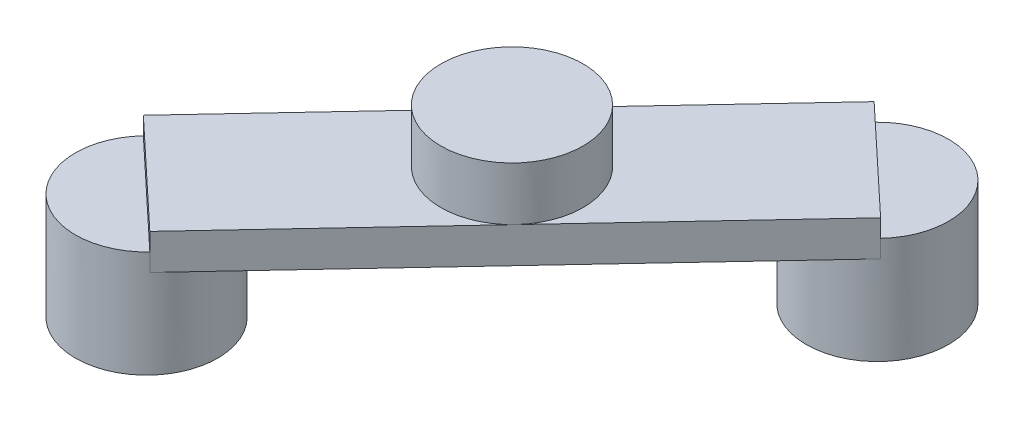
SolidWorks part; units mm, degrees
ref_plane "Front Plane" through (0, 0, 0) normal (0, 0, 1) x (1, 0, 0)
ref_plane "Top Plane" through (0, 0, 0) normal (0, 1, 0) x (1, 0, 0)
ref_plane "Right Plane" through (0, 0, 0) normal (1, 0, 0) x (0, 0, -1)
sketch "Sketch1" plane through (0, 0, 0) normal (0, 1, 0) x (1, 0, 0)
  line L0 (0, 0) -> (14.8833, -1.8676) construction
  line L1 (-14.2765, 6.7034) -> (-15.4901, -2.9683)
  line L2 (-15.4901, -2.9683) -> (-10.787, -11.5063)
  line L3 (-10.787, -11.5063) -> (-1.9637, -15.6492)
  line L4 (-1.9637, -15.6492) -> (7.6097, -13.8147)
  line L5 (7.6097, -13.8147) -> (14.2765, -6.7034)
  line L6 (14.2765, -6.7034) -> (15.4901, 2.9683)
  line L7 (15.4901, 2.9683) -> (10.787, 11.5063)
  line L8 (10.787, 11.5063) -> (1.9637, 15.6492)
  line L9 (1.9637, 15.6492) -> (-7.6097, 13.8147)
  line L10 (-7.6097, 13.8147) -> (-14.2765, 6.7034)
  line L11 (14.8833, -1.8676) -> (21.4363, -2.6898) construction
  line L12 (0, 0) -> (2.823, -14.732) construction
  line L13 (2.823, -14.732) -> (3.8609, -20.1481) construction
  line L14 (2.3263, -12.1398) -> (12.2645, -1.5389) construction
  circle A0 centre (0, 0) radius 15 construction
  circle A1 centre (2.3263, -12.1398) radius 2
  circle A2 centre (12.2645, -1.5389) radius 2
  dimension "D2" = 4
  dimension "D3" = 4
  dimension "D1" = 30
  dimension "D4" = 5
extrude "Boss-Extrude1" add sketch "Sketch1" along normal blind 3 contours A1 | A2
ref_plane "Plane1" through (8.7545, 0, 8.2072) normal (0.7295, 0, 0.6839) x (0.6839, 0, -0.7295)
sketch "Sketch2" plane through (8.7545, 0, 8.2072) normal (0.7295, 0, 0.6839) x (0.6839, 0, -0.7295)
  line L0 (9.2654, 3) -> (5.2654, 3) construction
  line L5 (9.2654, 3) -> (5.2654, 3)
  line L6 (-7.2654, 3) -> (7.2654, 3)
  line L7 (-5.2654, 3) -> (-9.2654, 3) construction
  line L9 (-7.2654, 2.5) -> (7.2654, 2.5)
  line L10 (-7.2654, 2.5) -> (-7.2654, 3.5)
  line L11 (-7.2654, 3.5) -> (7.2654, 3.5)
  line L12 (7.2654, 2.5) -> (7.2654, 3.5)
  line L13 (-7.2654, 2.5) -> (7.2654, 3.5) construction
  line L14 (-7.2654, 3.5) -> (7.2654, 2.5) construction
  point P0 (0, 3.0774)
  point P7 (0, 3)
  dimension "D1" = 1
extrude "Boss-Extrude2" add sketch "Sketch2" against normal blind 4 contours L5 L12 L11 L10 L6 | L9 L12 L5 L6 L10
sketch "Sketch4" plane through (0, 3.5, 0) normal (0, 1, 0) x (1, 0, 0)
  line L0 (0.8672, -10.7719) -> (3.7854, -13.5077) construction
  line L1 (0.8672, -10.7719) -> (10.8054, -0.1711) construction
  line L2 (0.8672, -10.7719) -> (3.7854, -13.5077)
  line L3 (0.8672, -10.7719) -> (10.8054, -0.1711)
  line L5 (10.8054, -0.1711) -> (13.7236, -2.9068) construction
  circle A0 centre (7.2954, -6.8394) radius 2
  point P5 (0, 0)
  point P7 (10.8266, -7.2938)
  dimension "D1" = 4
  dimension "D2" = 2
  dimension "D3" = 7.2654
  dimension "D4" = 7.2654
extrude "Boss-Extrude3" add sketch "Sketch4" along normal blind 1.5 contours A0
sketch "Sketch5" plane through (5.8363, 0, 5.4715) normal (-0.7295, 0, -0.6839) x (-0.6839, 0, 0.7295)
  line L0 (2, 5) -> (-2, 5) construction
  line L1 (-9.2654, 0) -> (-5.2654, 0) construction
  line L2 (2, 5) -> (-2, 5)
  line L3 (-9.2654, 0) -> (-5.2654, 0)
